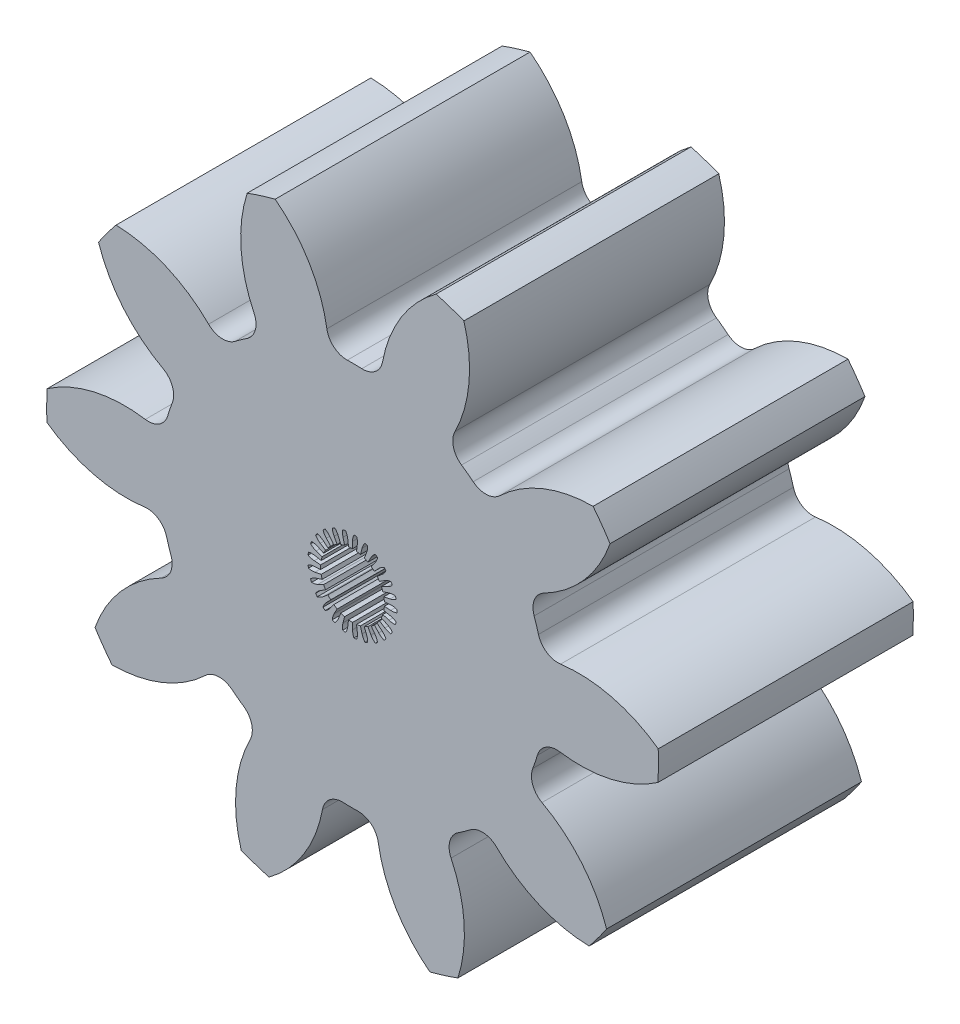
SolidWorks part; units mm, degrees
material "ABS"
ref_plane "Front" through (0, 0, 0) normal (0, 0, 1) x (1, 0, 0)
ref_plane "Top" through (0, 0, 0) normal (0, 1, 0) x (1, 0, 0)
ref_plane "Right" through (0, 0, 0) normal (1, 0, 0) x (0, 0, -1)
sketch "Sketch3" plane through (0, 0, 0) normal (0, 0, 1) x (1, 0, 0)
  circle A0 centre (0, 0) radius 15.24
  dimension "od" = 30.48
extrude "gearBody" add sketch "Sketch3" along normal blind 12.7
sketch "Sketch2" plane through (0, 0, 0) normal (0, 0, 1) x (1, 0, 0)
  line L0 (0, 0) -> (11.3595, 4.7053) construction
  line L1 (12.8367, -12.0857) -> (0, 0) construction
  line L2 (0, 0) -> (36.3143, 0) construction
  line L3 (12.544, -1.9847) -> (11.1917, -6.003) construction
  line L5 (11.8678, -3.9939) -> (0, 0) construction
  line L7 (0, 0) -> (12.2955, 0) construction
  arc A0 (12.1241, -2.0456) -> (10.8941, -5.7007) centre (0, 0) ccw construction
  arc A1 (15.214, -0.8896) -> (12.6563, -8.4897) centre (0, 0) ccw construction
  arc A2 (12.544, -1.9847) -> (11.1917, -6.003) centre (0, 0) ccw construction
  arc A3 (8.9781, -3.4023) -> (9.2084, -2.718) centre (0, 0) ccw
  arc A4 (12.8367, -12.0857) -> (9.4391, -4.6417) centre (6.2035, -10.6158) ccw
  arc A5 (12.8367, -12.0857) -> (17.5318, 1.8658) centre (0, 0) ccw
  arc A6 (17.5318, 1.8658) -> (10.3249, -2.0095) centre (11.3595, 4.7053) cw
  arc A7 (9.2084, -2.718) -> (10.3249, -2.0095) centre (10.1719, -3.0024) cw
  arc A8 (9.4391, -4.6417) -> (8.9781, -3.4023) centre (9.9175, -3.7583) cw
  point P6 (17.5318, 1.8658)
  point P22 (12.8367, -12.0857)
  dimension "baseDia" = 24.591
  dimension "od" = 30.48
  dimension "pd" = 25.4
  dimension "rd" = 19.2024
  dimension "rFillet" = 1.0046
  dimension "pointX" = 17.5318
  dimension "pointY" = 1.8658
  dimension "CTT" = 4.0183
  dimension "flankCenterAngle" = 22.5
extrude "toothCut" cut sketch "Sketch2" along normal through all
pattern_circular "CirPattern1" count 10 over 360 about axis through (0, 0, 0) along (0, 0, 1) of "toothCut"
sketch3d "3DSketch1" plane through (0, 0, 0) normal (0, 0, 1) x (1, 0, 0)
sketch "Sketch4" plane through (0, 0, 12.7) normal (0, 0, 1) x (1, 0, 0)
  line L0 (0, 0) -> (2.54, 0) construction
  line L1 (0, 0) -> (1.9012, 0.1196) construction
  line L2 (0, 0) -> (1.575, 0.199) construction
  line L3 (0, 0) -> (2.2214, 0.0698) construction
  line L4 (0, 0) -> (1.575, 0.199)
  line L5 (1.5844, 0.0997) -> (1.9012, 0.1196)
  line L6 (1.5844, -0.0997) -> (1.9012, -0.1196)
  line L7 (0, 0) -> (1.575, -0.199)
  circle A0 centre (0, 0) radius 1.5875 construction
  circle A1 centre (0, 0) radius 1.905 construction
  circle A2 centre (0, 0) radius 2.2225 construction
  arc A5 (1.9012, 0.1196) -> (2.2214, 0.0698) centre (1.9485, -0.6308) cw
  arc A6 (2.2214, 0.0698) -> (2.2214, -0.0698) centre (0, 0) cw
  arc A7 (1.575, 0.199) -> (1.5844, 0.0997) centre (0, 0) cw
  arc A8 (1.9012, -0.1196) -> (2.2214, -0.0698) centre (1.9485, 0.6308) ccw
  arc A9 (1.575, -0.199) -> (1.5844, -0.0997) centre (0, 0) ccw
  dimension "D1" = 3.175
  dimension "D2" = 3.81
  dimension "D3" = 4.445
  dimension "D4" = 7.2
  dimension "D5" = 1.8
  dimension "D6" = 3.6
extrude "Cut-Extrude1" cut sketch "Sketch4" against normal through all
pattern_circular "CirPattern2" count 25 every 14.4 about axis through (-0.0012, 0, 0) along (0, 0, 1) of "Cut-Extrude1"
sketch "Sketch5" plane through (0, 0, 12.7) normal (0, 0, 1) x (1, 0, 0)
  circle A0 centre (-0.0025, -0.0002) radius 1.5894
extrude "Cut-Extrude2" cut sketch "Sketch5" against normal through all
